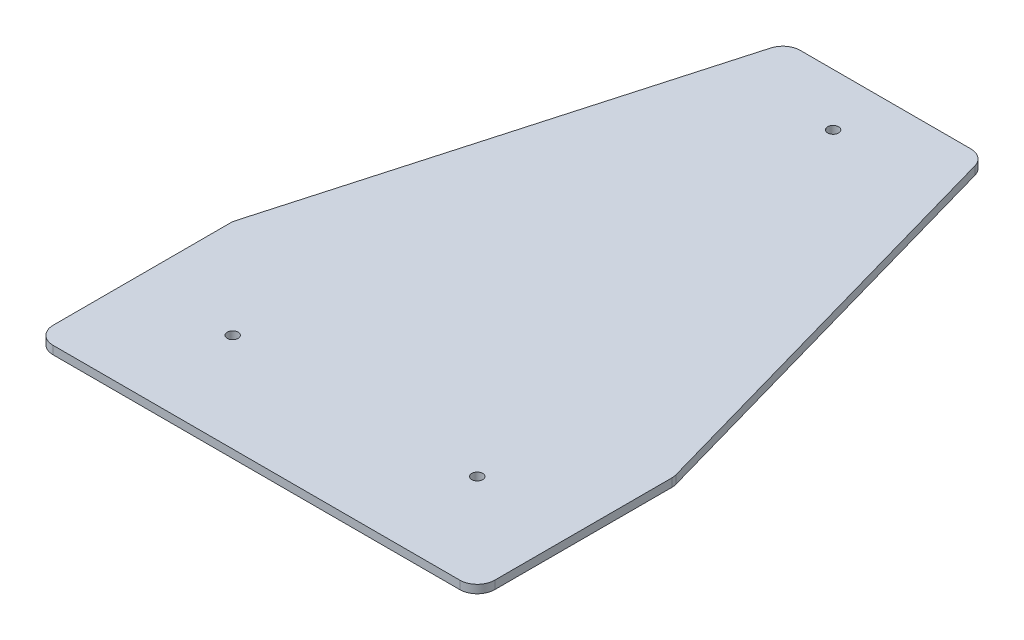
SolidWorks part; units mm, degrees
ref_plane "Front Plane" through (0, 0, 0) normal (0, 0, 1) x (1, 0, 0)
ref_plane "Top Plane" through (0, 0, 0) normal (0, 1, 0) x (1, 0, 0)
ref_plane "Right Plane" through (0, 0, 0) normal (1, 0, 0) x (0, 0, -1)
sketch "Sketch3" plane through (0, 0, 0) normal (0, 1, 0) x (1, 0, 0)
  line L0 (-28.18, 151.82) -> (-28.18, 28.18) construction
  line L1 (-63.18, -28.18) -> (63.18, -28.18)
  line L2 (-63.18, -28.18) -> (-63.18, 28.18)
  line L3 (-63.18, 28.18) -> (63.18, 28.18) construction
  line L4 (63.18, -28.18) -> (63.18, 28.18)
  line L5 (-63.18, -28.18) -> (63.18, 28.18) construction
  line L6 (-63.18, 28.18) -> (63.18, -28.18) construction
  line L7 (-28.18, 151.82) -> (28.18, 151.82)
  line L8 (-28.18, 28.18) -> (28.18, 28.18) construction
  line L9 (28.18, 151.82) -> (28.18, 28.18) construction
  line L10 (-28.18, 151.82) -> (28.18, 28.18) construction
  line L11 (-28.18, 28.18) -> (28.18, 151.82) construction
  line L12 (-28.18, 151.82) -> (-63.18, 28.18)
  line L14 (28.18, 151.82) -> (63.18, 28.18)
  point P0 (0, 0)
  point P7 (0, 90)
  dimension "D1" = 126.36
  dimension "D2" = 56.36
  dimension "D4" = 123.64
  dimension "D5" = 35
  dimension "D6" = 35
  dimension "D7" = 56.36
extrude "Boss-Extrude1" add sketch "Sketch3" along normal blind 2.36
fillet "Fillet1" radius 5 6 edges at (-63.18, 1.18, -28.18) (-28.18, 1.18, -151.82) (28.18, 1.18, -151.82) (63.18, 1.18, -28.18) (63.18, 1.18, 28.18) (-63.18, 1.18, 28.18)
sketch "Sketch4" plane through (0, 2.36, 0) normal (0, 1, 0) x (1, 0, 0)
  line L0 (24.3989, 151.82) -> (-24.3989, 151.82) construction
  line L1 (-58.18, -28.18) -> (58.18, -28.18) construction
  line L2 (-63.18, 27.4859) -> (-63.18, -23.18) construction
  line L3 (63.18, -23.18) -> (63.18, 27.4859) construction
  circle A0 centre (-35, 0) radius 1.5625
  circle A1 centre (35, 0) radius 1.5625
  circle A2 centre (0, 136.82) radius 1.5625
  dimension "D6" = 3.125
  dimension "D7" = 3.125
  dimension "D8" = 3.125
  dimension "D1" = 15
  dimension "D2" = 28.18
  dimension "D3" = 28.18
  dimension "D4" = 28.18
  dimension "D5" = 28.18
extrude "Cut-Extrude1" cut sketch "Sketch4" against normal through all
